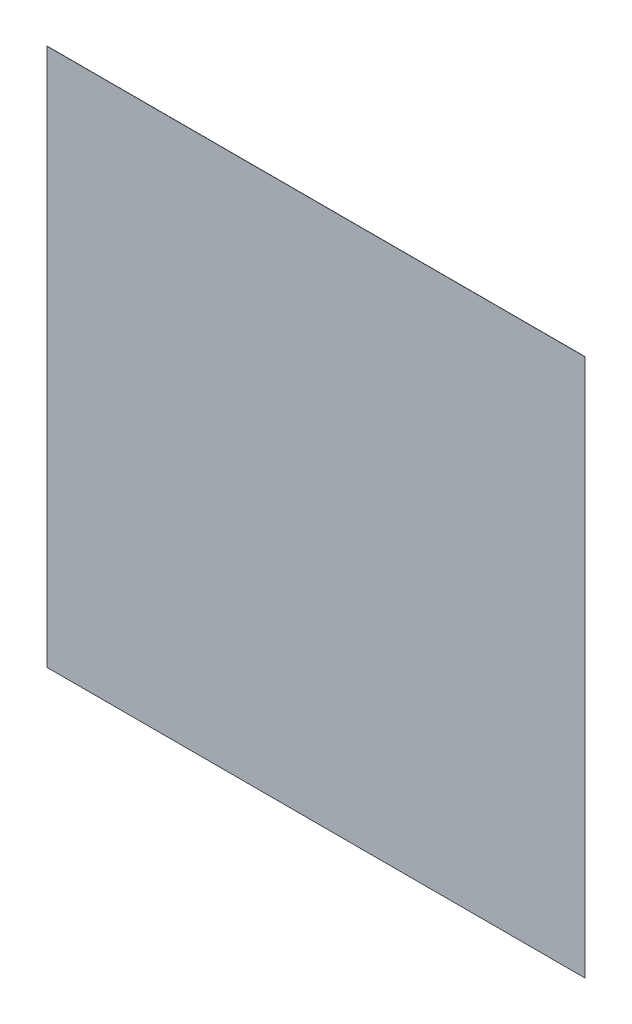
SolidWorks part; units mm, degrees
ref_plane "Front Plane" through (0, 0, 0) normal (0, 0, 1) x (1, 0, 0)
ref_plane "Top Plane" through (0, 0, 0) normal (0, 1, 0) x (1, 0, 0)
ref_plane "Right Plane" through (0, 0, 0) normal (1, 0, 0) x (0, 0, -1)
sketch "Sketch1" plane through (0, 0, 0) normal (0, 0, 1) x (1, 0, 0)
  line L0 (0, 0) -> (0, 152.4) construction
  line L1 (-152.4, 152.4) -> (152.4, 152.4)
  line L2 (-152.4, 152.4) -> (-152.4, -152.4)
  line L3 (-152.4, -152.4) -> (152.4, -152.4)
  line L4 (152.4, 152.4) -> (152.4, -152.4)
  line L5 (0, 0) -> (152.4, 0) construction
  dimension "D1" = 304.8
  dimension "D2" = 304.8
extrude "Boss-Extrude1" add sketch "Sketch1" against normal blind 0.1
